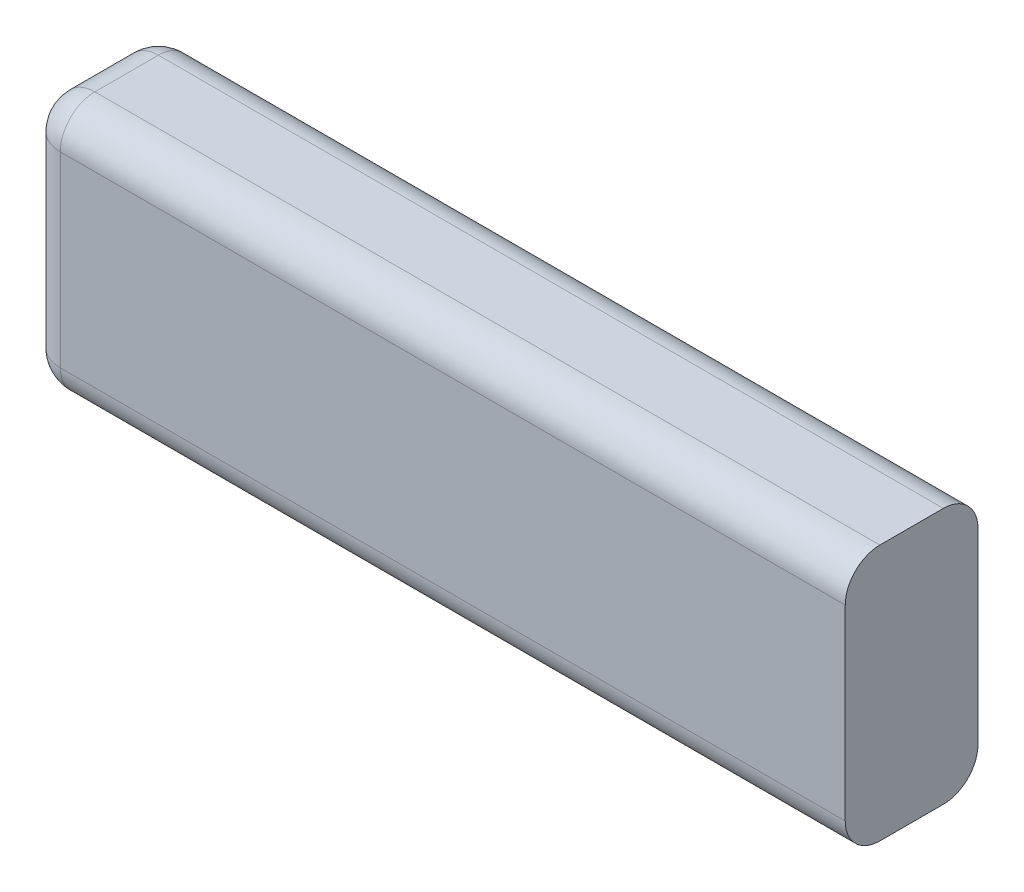
SolidWorks part; units mm, degrees
ref_plane "Front" through (0, 0, 0) normal (0, 0, 1) x (1, 0, 0)
ref_plane "Top" through (0, 0, 0) normal (0, 1, 0) x (1, 0, 0)
ref_plane "Right" through (0, 0, 0) normal (1, 0, 0) x (0, 0, -1)
sketch "Sketch1" plane through (0, 0, 0) normal (0, 0, 1) x (1, 0, 0)
  line L1 (0, 0) -> (35.5, 0)
  line L2 (0, 0) -> (0, 11.1)
  line L3 (0, 11.1) -> (35.5, 11.1)
  line L4 (35.5, 0) -> (35.5, 11.1)
  dimension "D1" = 11.1
  dimension "D2" = 35.5
extrude "Boss-Extrude1" add sketch "Sketch1" along normal blind 5.75
fillet "Fillet1" radius 1.5 8 edges at (17.75, 0, 0) (17.75, 0, 5.75) (0, 0, 2.875) (0, 5.55, 0) (0, 5.55, 5.75) (17.75, 11.1, 0) (17.75, 11.1, 5.75) (0, 11.1, 2.875)
